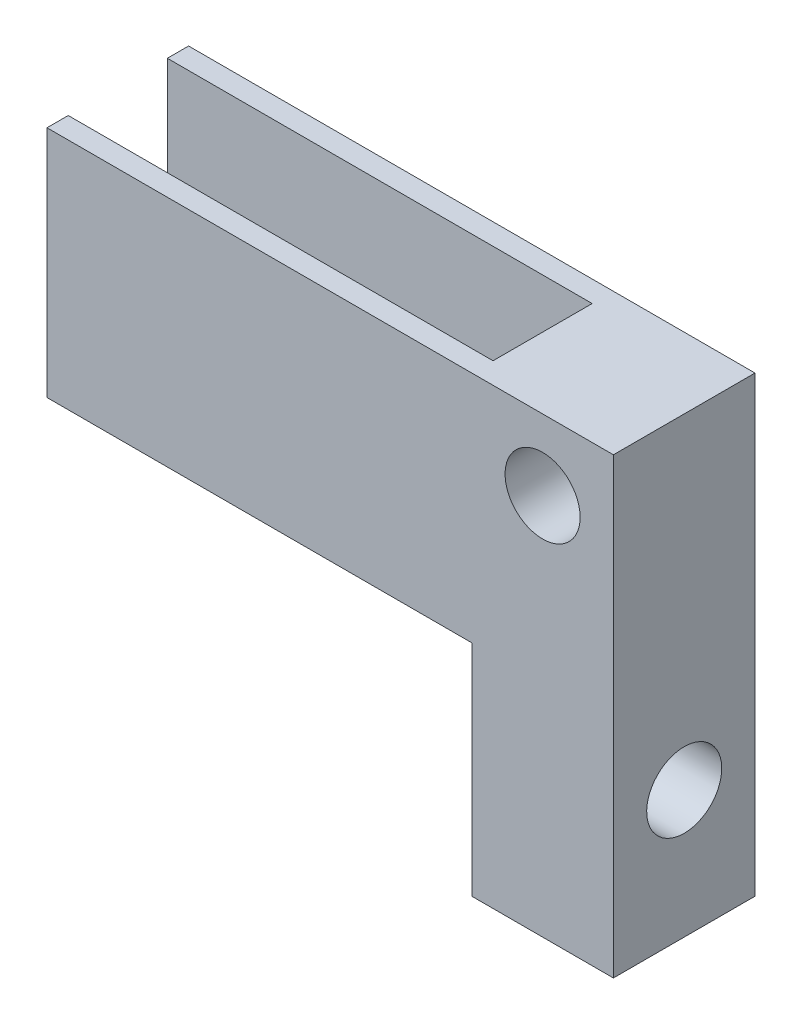
SolidWorks part; units mm, degrees
ref_plane "Front Plane" through (0, 0, 0) normal (0, 0, 1) x (1, 0, 0)
ref_plane "Top Plane" through (0, 0, 0) normal (0, 1, 0) x (1, 0, 0)
ref_plane "Right Plane" through (0, 0, 0) normal (1, 0, 0) x (0, 0, -1)
sketch "Sketch2" plane through (0, 0, 0) normal (0, 0, 1) x (1, 0, 0)
  line L8 (0, 0) -> (0, 50)
  line L9 (0, 50) -> (10, 50)
  line L10 (10, 50) -> (10, 0)
  line L11 (10, 0) -> (0, 0)
  dimension "D1" = 50
  dimension "D2" = 10
extrude "Boss-Extrude1" add sketch "Sketch2" along normal blind 10 contours L11 L8 L9 L10
sketch "Sketch6" plane through (0, 0, 10) normal (0, 0, 1) x (1, 0, 0)
  line L0 (10, 50) -> (10, 0) construction
  line L1 (10, 0) -> (0, 0) construction
  circle A0 centre (5, 27) radius 2.65
  dimension "D1" = 5.3
  dimension "D2" = 5
  dimension "D3" = 27
extrude "Cut-Extrude3" cut sketch "Sketch6" against normal through all contours A0
sketch "Sketch7" plane through (0, 0, 0) normal (-1, 0, 0) x (0, 0, 1)
  line L0 (10, 0) -> (10, 50) construction
  line L1 (10, 0) -> (0, 0) construction
  circle A0 centre (5, 41) radius 2.35
  circle A1 centre (5, 9) radius 2.65
  dimension "D3" = 4.7
  dimension "D4" = 5.3
  dimension "D5" = 9
  dimension "D1" = 32
  dimension "D2" = 5
  dimension "D6" = 5
extrude "Cut-Extrude4" cut sketch "Sketch7" against normal through all
sketch "Sketch8" plane through (0, 0, 0) normal (-1, 0, 0) x (0, 0, 1)
  line L0 (8.5, 36.5) -> (8.5, 15.5)
  line L1 (8.5, 15.5) -> (10, 15.5)
  line L2 (10, 0) -> (10, 50) construction
  line L3 (10, 15.5) -> (10, 36.5)
  line L4 (10, 36.5) -> (8.5, 36.5)
  line L5 (1.5, 36.5) -> (1.5, 15.5)
  line L6 (1.5, 15.5) -> (0, 15.5)
  line L7 (0, 0) -> (0, 50) construction
  line L8 (0, 15.5) -> (0, 36.5)
  line L9 (0, 36.5) -> (1.5, 36.5)
  line L10 (10, 50) -> (0, 50) construction
  dimension "D1" = 1.5
  dimension "D2" = 1.5
  dimension "D3" = 13.5
  dimension "D4" = 21
extrude "Boss-Extrude2" add sketch "Sketch8" along normal blind 30
sketch "Sketch9" plane through (0, 0, 10) normal (0, 0, 1) x (1, 0, 0)
  line L0 (10, 0) -> (0, 0) construction
  line L1 (-34.1392, 32) -> (18.855, 32)
  line L2 (-34.1392, 32) -> (-34.1392, 51.0598)
  line L3 (-34.1392, 51.0598) -> (18.855, 51.0598)
  line L4 (18.855, 32) -> (18.855, 51.0598)
  dimension "D1" = 32
extrude "Cut-Extrude5" cut sketch "Sketch9" against normal through all
